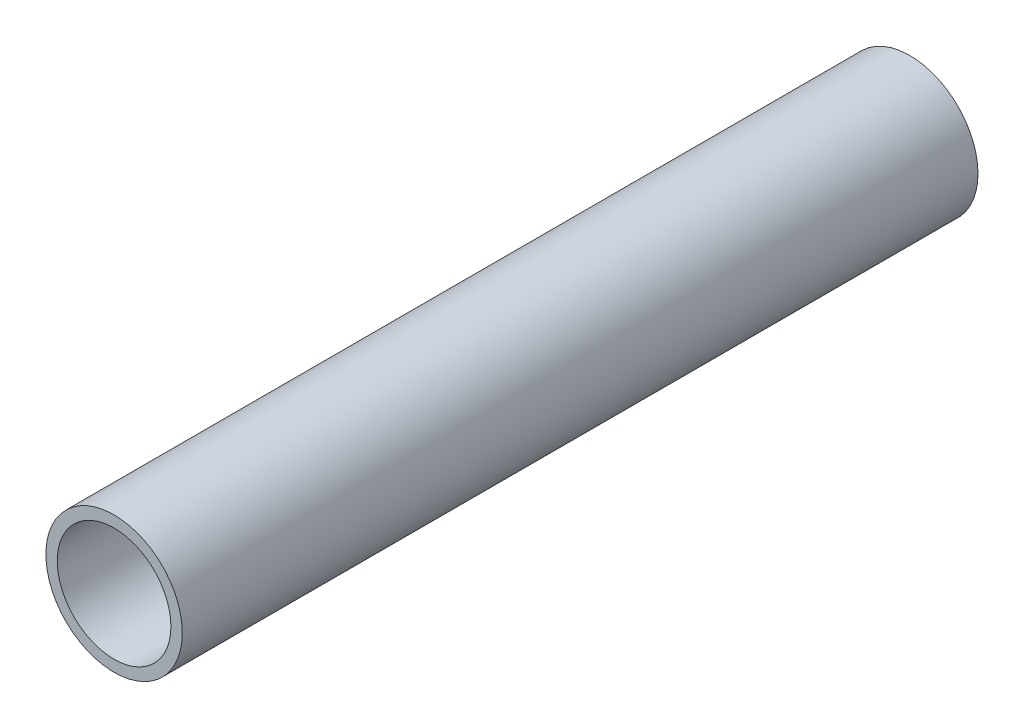
SolidWorks part; units mm, degrees
ref_plane "Piano frontale" through (0, 0, 0) normal (0, 0, 1) x (1, 0, 0)
ref_plane "Piano superiore" through (0, 0, 0) normal (0, 1, 0) x (1, 0, 0)
ref_plane "Piano destro" through (0, 0, 0) normal (1, 0, 0) x (0, 0, -1)
sketch "Schizzo1" plane through (0, 0, 0) normal (0, 0, 1) x (1, 0, 0)
  circle A0 centre (0, 0) radius 12
  circle A1 centre (0, 0) radius 10
  dimension "D1" = 24
  dimension "D2" = 20
extrude "Estrusione-Estrusione1" add sketch "Schizzo1" along normal blind 140
cosmetic thread "Filettatura cosmetica1" parameters "D1"=15, "D2"=22
cosmetic thread "Filettatura cosmetica2" parameters "D1"=15, "D2"=22
cosmetic thread "Filettatura cosmetica3" parameters "D1"=15, "D2"=20.704
cosmetic thread "Filettatura cosmetica4" parameters "D1"=15, "D2"=20.704
